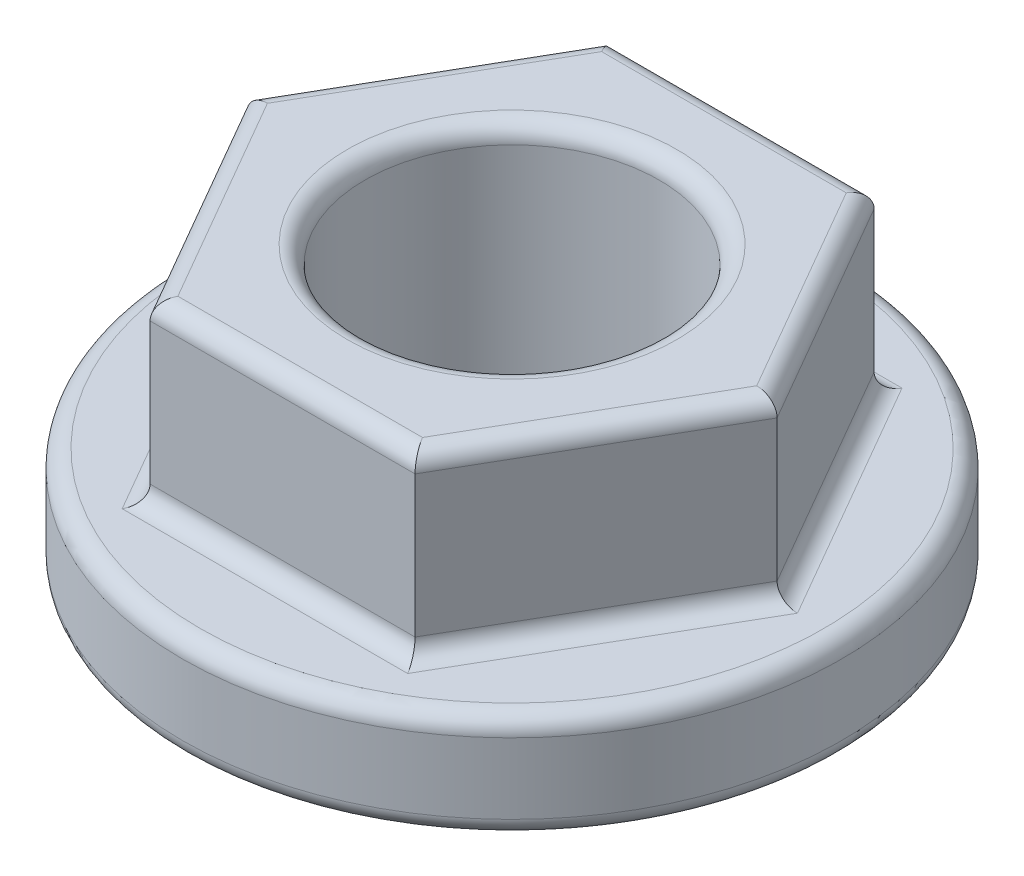
SolidWorks part; units mm, degrees
ref_plane "Front Plane" through (0, 0, 0) normal (0, 0, 1) x (1, 0, 0)
ref_plane "Top Plane" through (0, 0, 0) normal (0, 1, 0) x (1, 0, 0)
ref_plane "Right Plane" through (0, 0, 0) normal (1, 0, 0) x (0, 0, -1)
sketch "Sketch1" plane through (0, 0, 0) normal (0, 1, 0) x (1, 0, 0)
  circle A0 centre (0, 0) radius 5.6
  dimension "D1" = 11.2
extrude "Boss-Extrude1" add sketch "Sketch1" along normal blind 4.8
sketch "Sketch2" plane through (0, 4.8, 0) normal (0, 1, 0) x (1, 0, 0)
  circle A0 centre (0, 0) radius 2.5
  dimension "D1" = 5
extrude "Cut-Extrude1" cut sketch "Sketch2" against normal blind 4.8
sketch "Sketch3" plane through (0, 4.8, 0) normal (0, 1, 0) x (1, 0, 0)
  line L1 (4.5033, 0) -> (2.2517, 3.9)
  line L2 (2.2517, 3.9) -> (-2.2517, 3.9)
  line L3 (-2.2517, 3.9) -> (-4.5033, 0)
  line L4 (-4.5033, 0) -> (-2.2517, -3.9)
  line L5 (-2.2517, -3.9) -> (2.2517, -3.9)
  line L6 (2.2517, -3.9) -> (4.5033, 0)
  circle A0 centre (0, 0) radius 3.9 construction
  dimension "D1" = 7.8
extrude "Cut-Extrude2" cut sketch "Sketch3" against normal blind 3 flip side to cut
fillet "Fillet1" radius 0.3 16 edges at (0, 0, 5.6) (0, 0, 2.5) (0, 1.8, 5.6) (3.3775, 1.8, 1.95) (3.3775, 1.8, -1.95) (0, 1.8, -3.9) (-3.3775, 1.8, -1.95) (-3.3775, 1.8, 1.95) (0, 1.8, 3.9) (-3.3775, 4.8, 1.95) (-3.3775, 4.8, -1.95) (0, 4.8, -3.9) (3.3775, 4.8, -1.95) (3.3775, 4.8, 1.95) (0, 4.8, 3.9) (0, 4.8, 2.5)
